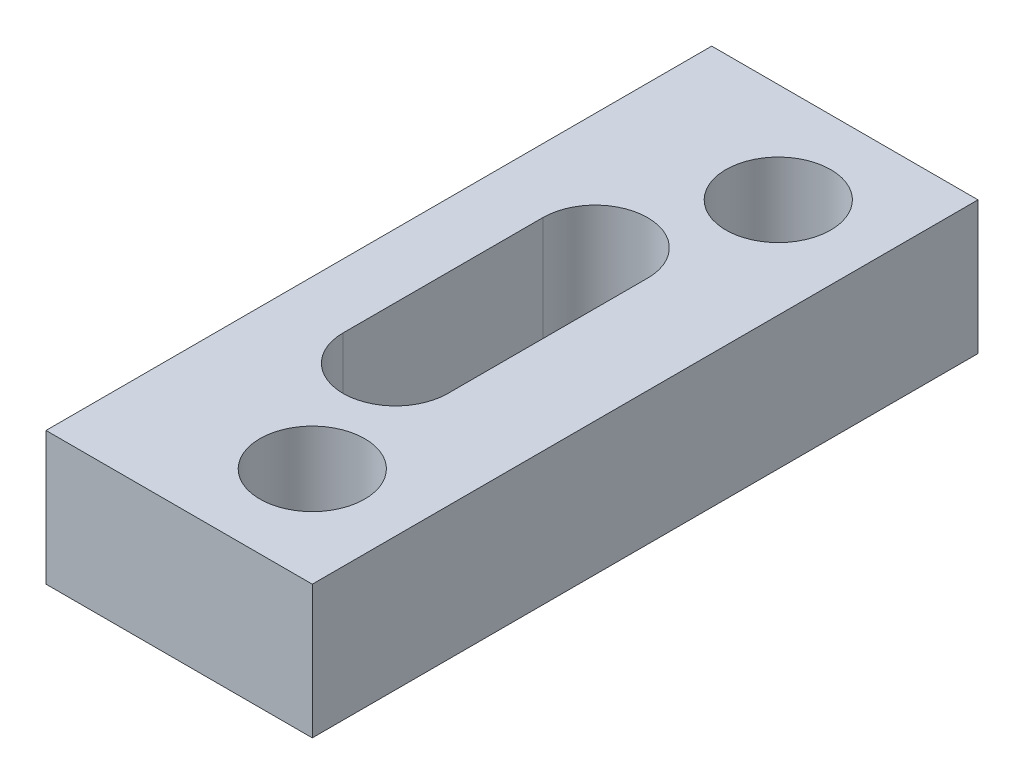
SolidWorks part; units mm, degrees
material "ABS"
ref_plane "Front Plane" through (0, 0, 0) normal (0, 0, 1) x (1, 0, 0)
ref_plane "Top Plane" through (0, 0, 0) normal (0, 1, 0) x (1, 0, 0)
ref_plane "Right Plane" through (0, 0, 0) normal (1, 0, 0) x (0, 0, -1)
sketch "Sketch1" plane through (0, 0, 0) normal (0, 1, 0) x (1, 0, 0)
  line L0 (3.5, 7) -> (3.5, 13) construction
  line L1 (1.925, 7) -> (1.925, 13)
  line L2 (0, 20) -> (0, 0)
  line L3 (0, 0) -> (8, 0)
  line L4 (8, 0) -> (8, 20)
  line L5 (8, 20) -> (0, 20)
  line L6 (0, 10) -> (8, 10) construction
  line L7 (5.075, 7) -> (5.075, 13)
  circle A0 centre (5, 17) radius 1.575
  circle A1 centre (5, 3) radius 1.575
  arc A2 (1.925, 7) -> (5.075, 7) centre (3.5, 7) ccw
  arc A3 (5.075, 13) -> (1.925, 13) centre (3.5, 13) ccw
  point P6 (3.5, 10)
  dimension "D3" = 3.15
  dimension "D8" = 1.575
  dimension "D1" = 8
  dimension "D2" = 20
  dimension "D4" = 14
  dimension "D5" = 6
  dimension "D6" = 1.5
  dimension "D7" = 3.5
extrude "Boss-Extrude1" add sketch "Sketch1" against normal blind 4
